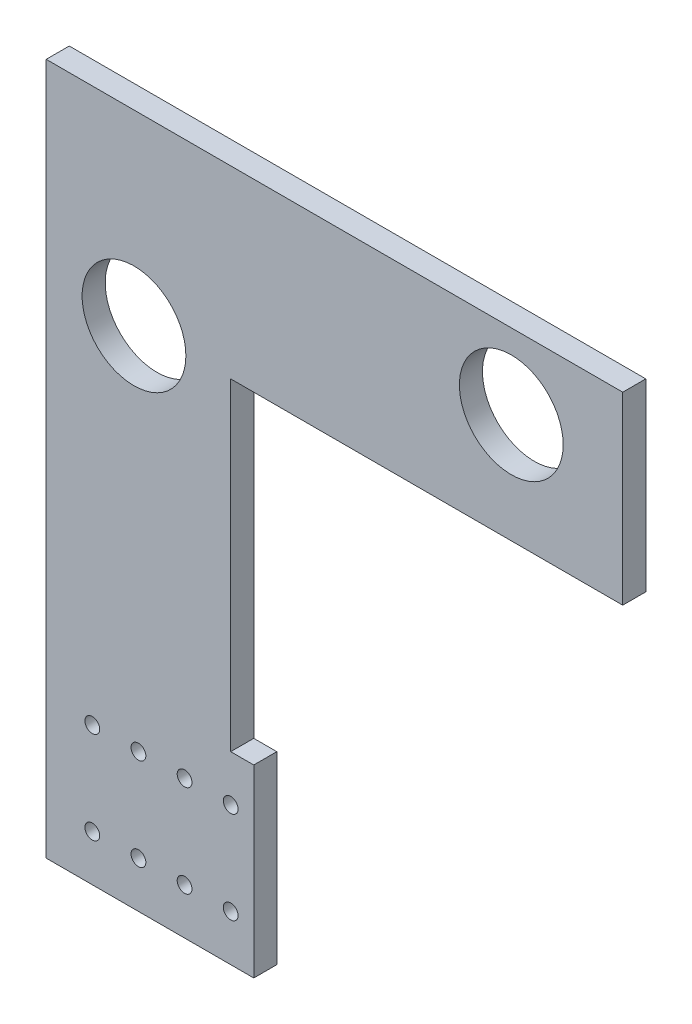
SolidWorks part; units mm, degrees
ref_plane "Front Plane" through (0, 0, 0) normal (0, 0, 1) x (1, 0, 0)
ref_plane "Top Plane" through (0, 0, 0) normal (0, 1, 0) x (1, 0, 0)
ref_plane "Right Plane" through (0, 0, 0) normal (1, 0, 0) x (0, 0, -1)
sketch "Sketch2" plane through (0, 0, 0) normal (0, 0, 1) x (1, 0, 0)
  line L0 (-125.792, -159.6416) -> (-74.992, -159.6416)
  line L2 (-74.992, -19.9416) -> (32.958, -19.9416)
  line L3 (32.958, -19.9416) -> (32.958, 30.8584)
  line L4 (32.958, 30.8584) -> (-125.792, 30.8584)
  line L9 (-125.792, 30.8584) -> (-125.792, -140.5916)
  line L10 (-125.792, -140.5916) -> (-125.792, -159.6416)
  line L11 (-74.992, -159.6416) -> (-68.642, -159.6416)
  line L12 (-68.642, -159.6416) -> (-68.642, -108.8416)
  line L13 (-68.642, -108.8416) -> (-74.992, -108.8416)
  line L14 (-74.992, -19.9416) -> (-74.992, -108.8416)
  dimension "D1" = 50.8
  dimension "D2" = 139.7
  dimension "D3" = 107.95
  dimension "D4" = 50.8
  dimension "D5" = 6.35
  dimension "D6" = 50.8
extrude "Boss-Extrude1" add sketch "Sketch2" along normal blind 6.35
sketch "Sketch3" plane through (0, 0, 6.35) normal (0, 0, 1) x (1, 0, 0)
  circle A0 centre (-101.6191, -20.6122) radius 14.2875
  circle A1 centre (2.2669, 10.1218) radius 14.2875
  circle A2 centre (-87.692, -146.9416) radius 2.032
  circle A4 centre (-113.092, -146.9416) radius 2.032
  circle A5 centre (-100.392, -146.9416) radius 2.032
  circle A6 centre (-74.992, -146.9416) radius 2.032
  circle A7 centre (-113.092, -121.5416) radius 2.032
  circle A8 centre (-87.692, -121.5416) radius 2.032
  circle A9 centre (-74.992, -121.5416) radius 2.032
  circle A10 centre (-100.392, -121.5416) radius 2.032
  dimension "D1" = 28.575
  dimension "D4" = 28.575
  dimension "D5" = 4.064
  dimension "D8" = 4.064
  dimension "D9" = 4.064
  dimension "D10" = 4.064
  dimension "D3" = 4.064
  dimension "D7" = 4.064
  dimension "D6" = 4.064
  dimension "D11" = 4.064
  dimension "D2" = 12.7
extrude "Cut-Extrude1" cut sketch "Sketch3" against normal blind 6.35
sketch "Sketch4" plane through (0, 0, 6.35) normal (0, 0, 1) x (1, 0, 0)
  circle A0 centre (-113.092, -146.9416) radius 2.032
  circle A1 centre (-100.392, -146.9416) radius 2.032
  circle A2 centre (-87.692, -146.9416) radius 2.032
  circle A3 centre (-74.992, -146.9416) radius 2.032
